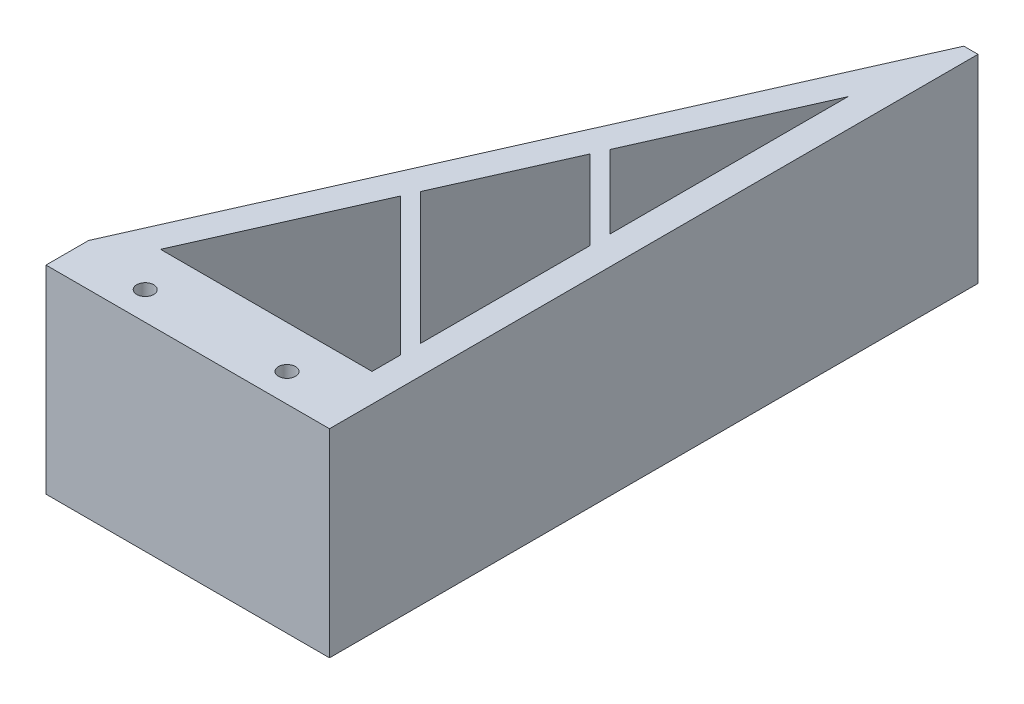
SolidWorks part; units mm, degrees
ref_plane "Front Plane" through (0, 0, 0) normal (0, 0, 1) x (1, 0, 0)
ref_plane "Top Plane" through (0, 0, 0) normal (0, 1, 0) x (1, 0, 0)
ref_plane "Right Plane" through (0, 0, 0) normal (1, 0, 0) x (0, 0, -1)
sketch "Sketch1" plane through (0, 0, 0) normal (0, 1, 0) x (1, 0, 0)
  line L0 (-10.2821, -23.1346) -> (8.7179, 19.6154)
  line L4 (9.7179, -23.1346) -> (9.7179, 19.6154)
  line L5 (-10.2821, -23.1346) -> (8.7179, 19.6154) construction
  line L6 (7.7179, -21.1346) -> (7.7179, 12.4409)
  line L7 (-7.2045, -21.1346) -> (7.7179, 12.4409)
  line L8 (-7.2045, -21.1346) -> (7.7179, -21.1346)
  line L9 (8.7179, 19.6154) -> (9.7179, 19.6154)
  line L10 (9.7179, -23.1346) -> (9.7179, 21.8654) construction
  line L12 (-10.2821, -23.1346) -> (-10.2821, -26.1346)
  line L13 (-10.2821, -26.1346) -> (9.7179, -26.1346)
  line L14 (9.7179, -23.1346) -> (9.7179, -26.1346)
  line L15 (-10.2821, -23.1346) -> (9.7179, -23.1346) construction
  line L16 (-10.2821, -23.1346) -> (9.7179, 21.8654) construction
  point P0 (0, 0)
  dimension "D1" = 2
  dimension "D2" = 42.75
  dimension "D3" = 20
  dimension "D4" = 1
  dimension "D7" = 20
  dimension "D8" = 3
sketch "Sketch2" plane through (0, 0, 0) normal (0, 1, 0) x (1, 0, 0)
  line L0 (7.7179, -19.1346) -> (-1.9976, -9.4191)
  line L1 (7.7179, -21.1346) -> (7.7179, 12.4409) construction
  line L2 (-7.2045, -21.1346) -> (7.7179, 12.4409) construction
  line L3 (-1.9976, -9.4191) -> (-1.5625, -8.44)
  line L4 (-1.5625, -8.44) -> (7.7179, -17.7204)
  line L5 (7.7179, -17.7204) -> (7.7179, -19.1346)
  line L6 (7.7179, -5.7611) -> (2.1173, -0.1605)
  line L7 (2.1173, -0.1605) -> (2.5525, 0.8186)
  line L8 (2.5525, 0.8186) -> (7.7179, -4.3469)
  line L9 (7.7179, -4.3469) -> (7.7179, -5.7611)
  line L10 (7.7179, -19.1346) -> (-28.0468, -19.1346) construction
  line L11 (7.7179, -5.7611) -> (-13.6676, -5.7611) construction
  dimension "D1" = 2
  dimension "D2" = 1
  dimension "D3" = 1
  dimension "D4" = 45
  dimension "D5" = 45
  dimension "D6" = 11.9594
extrude "Boss-Extrude1" add sketch "Sketch2" along normal blind 14
extrude "Boss-Extrude2" add sketch "Sketch1" along normal blind 14
sketch "Sketch3" plane through (0, 14, 0) normal (0, 1, 0) x (1, 0, 0)
  line L0 (-10.2821, -26.1346) -> (9.7179, -26.1346) construction
  line L1 (-10.2821, -23.1346) -> (-10.2821, -26.1346) construction
  circle A0 centre (4.7179, -24.1346) radius 0.6
  circle A1 centre (-5.2821, -24.1346) radius 0.6
  point P8 (0, 0)
  dimension "D1" = 1.2
  dimension "D2" = 1.2
  dimension "D3" = 2
  dimension "D4" = 2
  dimension "D5" = 5
  dimension "D6" = 10
extrude "Cut-Extrude1" cut sketch "Sketch3" against normal through all
